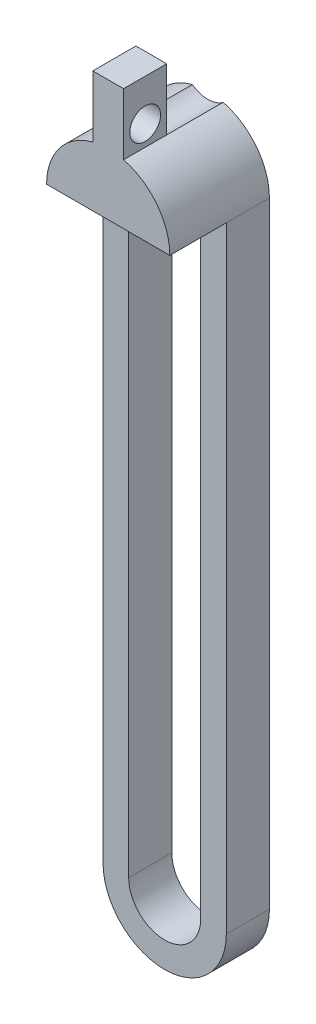
SolidWorks part; units mm, degrees
material "ABS"
ref_plane "前视基准面" through (0, 0, 0) normal (0, 0, 1) x (1, 0, 0)
ref_plane "上视基准面" through (0, 0, 0) normal (0, 1, 0) x (1, 0, 0)
ref_plane "右视基准面" through (0, 0, 0) normal (1, 0, 0) x (0, 0, -1)
sketch "草图1" plane through (0, 0, 0) normal (0, 0, 1) x (1, 0, 0)
  line L0 (0, 3.1738) -> (0, -56.8262) construction
  line L1 (3.505, 3.1738) -> (3.505, -56.8262)
  line L2 (-3.505, 3.1738) -> (-3.505, -56.8262)
  line L3 (0, 3.1738) -> (0, -56.8262) construction
  line L4 (6.005, 3.1738) -> (6.005, -56.8262)
  line L5 (-6.005, 3.1738) -> (-6.005, -56.8262)
  line L6 (-1.5, 8.9884) -> (-1.5, 14.9884)
  line L7 (-1.5, 14.9884) -> (1.5, 14.9884)
  line L8 (1.5, 14.9884) -> (1.5, 8.9884)
  line L9 (7.5896, -56.8262) -> (-8.7837, -56.8262) construction
  arc A0 (3.505, 3.1738) -> (-3.505, 3.1738) centre (0, 3.1738) ccw
  arc A1 (-3.505, -56.8262) -> (3.505, -56.8262) centre (0, -56.8262) ccw
  arc A2 (6.005, 3.1738) -> (1.5, 8.9884) centre (0, 3.1738) ccw
  arc A3 (-6.005, -56.8262) -> (6.005, -56.8262) centre (0, -56.8262) ccw
  arc A4 (-1.5, 8.9884) -> (-6.005, 3.1738) centre (0, 3.1738) ccw
  point P3 (0, -26.8262)
  point P10 (0, -9.8262)
  dimension "D1" = 60
  dimension "D2" = 7.01
  dimension "D3" = 2.5
  dimension "D4" = 3
  dimension "D5" = 1.5
  dimension "D6" = 6
extrude "凸台-拉伸1" add sketch "草图1" along normal blind 4.2
sketch "草图2" plane through (0, 0, 4.2) normal (0, 0, 1) x (1, 0, 0)
  line L0 (1.5, 14.9884) -> (-1.5, 14.9884)
  line L1 (-1.5, 14.9884) -> (-1.5, 8.9884)
  line L2 (-6.005, 3.1738) -> (6.005, 3.1738)
  line L3 (1.5, 8.9884) -> (1.5, 14.9884)
  arc A0 (-6.005, 3.1738) -> (-1.5, 8.9884) centre (0, 3.1738) cw
  arc A1 (-1.5, 8.9884) -> (-6.005, 3.1738) centre (0, 3.1738) ccw construction
  arc A2 (6.005, 3.1738) -> (1.5, 8.9884) centre (0, 3.1738) ccw construction
  arc A3 (1.5, 8.9884) -> (6.005, 3.1738) centre (0, 3.1738) cw
extrude "凸台-拉伸2" add sketch "草图2" along normal blind 5.5
sketch "草图3" plane through (0, 0, 0) normal (0, 0, -1) x (-1, 0, 0)
  line L1 (-1.5, 14.9884) -> (1.5, 14.9884)
  line L2 (-1.5, 14.9884) -> (-1.5, 8.9884)
  line L4 (1.5, 14.9884) -> (1.5, 8.9884)
  arc A1 (-1.5, 8.9884) -> (1.5, 8.9884) centre (0, 10.9884) ccw
  dimension "D1" = 2.5
extrude "切除-拉伸1" cut sketch "草图3" against normal blind 5.5
sketch "草图4" plane through (1.5, 0, 0) normal (1, 0, 0) x (0, 0, -1)
  line L0 (-9.7, 14.9884) -> (-5.5, 14.9884) construction
  line L1 (-7.6, 16.2236) -> (-7.6, 7.8145) construction
  circle A0 centre (-7.6, 10.9884) radius 1.5
  dimension "D1" = 3
  dimension "D2" = 4
extrude "切除-拉伸2" cut sketch "草图4" against normal blind 10
